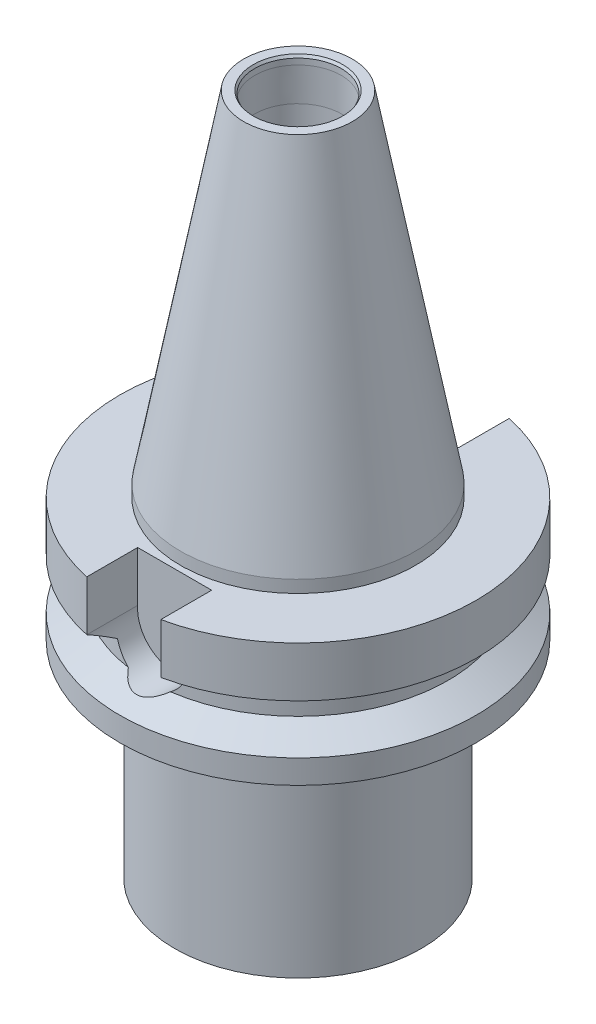
SolidWorks part; units mm, degrees
ref_plane "前视基准面" through (0, 0, 0) normal (0, 0, 1) x (1, 0, 0)
ref_plane "上视基准面" through (0, 0, 0) normal (0, 1, 0) x (1, 0, 0)
ref_plane "右视基准面" through (0, 0, 0) normal (1, 0, 0) x (0, 0, -1)
sketch "草图1" plane through (0, 0, 0) normal (0, 0, 1) x (1, 0, 0)
  line L0 (0, 104.8926) -> (0, -94.858) construction
  line L1 (-13.2096, 98.6358) -> (-28.575, 15.8358)
  line L2 (-28.575, 15.8358) -> (-28.575, 12.8358)
  line L3 (-28.575, 12.8358) -> (-43.3133, 12.8358)
  line L4 (-43.3133, 12.8358) -> (-43.3133, 0.6358)
  line L5 (-43.3133, 0.6358) -> (-36.5, -3.2978)
  line L6 (-13.2096, 98.6358) -> (-10.8684, 98.6358)
  line L7 (-36.5, -7.4306) -> (-43.3133, -11.3642)
  line L8 (-43.3133, -11.3642) -> (-43.3133, -17.1642)
  line L9 (-43.3133, -17.1642) -> (-30, -17.1642)
  line L10 (-30, -17.1642) -> (-30, -67.1642)
  line L11 (-36.5, -3.2978) -> (-36.5, -7.4306)
  line L12 (-10.5, 96.5497) -> (-10.5, 97.9977)
  line L13 (-10.7277, 88.231) -> (-10.7277, 46.4119)
  line L14 (-10.7277, 46.4119) -> (-9.4869, 45.6955)
  line L15 (-9.4869, 45.6955) -> (-9.4869, 31.1053)
  line L16 (-9.4869, 31.1053) -> (0, 25.628)
  line L17 (-10.8684, 98.6358) -> (-10.5, 97.9977)
  line L18 (-10.5, 96.5497) -> (-10.7277, 88.231)
  line L19 (-30, -67.1642) -> (-20.5, -67.1642)
  line L20 (0, -67.1642) -> (0, 25.628)
  line L21 (-20.5, -67.1642) -> (-16, -31.1642)
  line L22 (-16, -31.1642) -> (0, -31.1642)
  dimension "D2" = 3
  dimension "D3" = 120
  dimension "D4" = 73
  dimension "D5" = 82.8
  dimension "D6" = 5.8
  dimension "D7" = 12.2
  dimension "D8" = 12
  dimension "D9" = 30
  dimension "D10" = 50
  dimension "D11" = 10.5
  dimension "D12" = 13.2096
  dimension "D13" = 30
  dimension "D14" = 120
  dimension "D15" = 20.5
  dimension "D16" = 16
  dimension "D17" = 36
revolve "旋转2" add sketch "草图1" angle 360 about L0
cosmetic thread "装饰螺纹线3" parameters "D2"=58.376
ref_plane "基准面1" through (0, 0, 50) normal (0, 0, 1) x (1, 0, 0)
sketch "草图3" plane through (0, 0, 50) normal (0, 0, 1) x (1, 0, 0)
  line L0 (0, 50.9079) -> (0, -41.8052) construction
  line L1 (-9, 12.8358) -> (-9, 0.6358)
  line L2 (43.3133, 12.8358) -> (-43.3133, 12.8358) construction
  line L3 (-43.3133, 0.6358) -> (43.3133, 0.6358) construction
  line L4 (9, 0.6358) -> (9, 12.8358)
  line L5 (9, 12.8358) -> (-9, 12.8358)
  arc A0 (-9, 0.6358) -> (9, 0.6358) centre (0, 0) ccw
  dimension "D1" = 9
extrude "切除-拉伸1" cut sketch "草图3" against normal blind 20
mirror "镜向1" about plane through (0, 0, 0) normal (0, 0, 1) of "切除-拉伸1"
